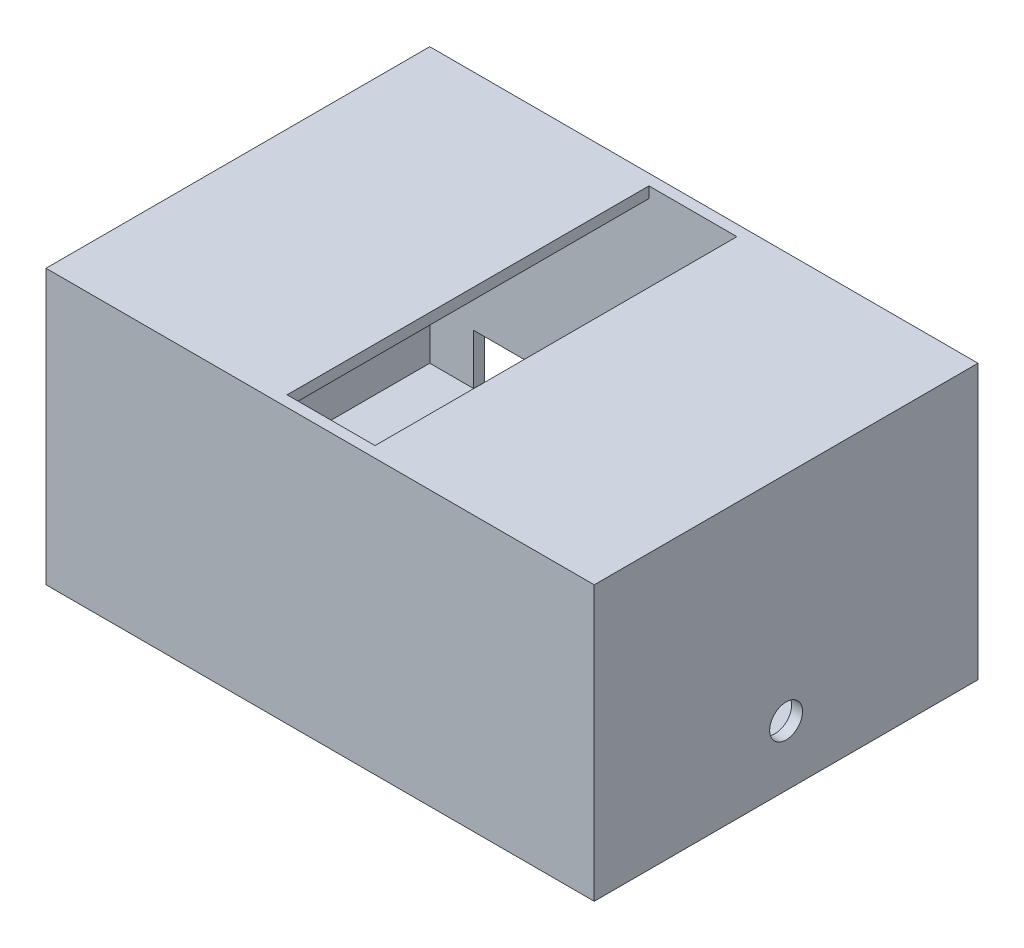
SolidWorks part; units mm, degrees
ref_plane "Front Plane" through (0, 0, 0) normal (0, 0, 1) x (1, 0, 0)
ref_plane "Top Plane" through (0, 0, 0) normal (0, 1, 0) x (1, 0, 0)
ref_plane "Right Plane" through (0, 0, 0) normal (1, 0, 0) x (0, 0, -1)
sketch "Sketch1" plane through (0, 0, 0) normal (0, 1, 0) x (1, 0, 0)
  line L0 (250, 0) -> (0, 0) construction
  line L1 (0, 0) -> (-250, 0) construction
  line L2 (-125, -87.5) -> (125, -87.5)
  line L3 (-125, -87.5) -> (-125, 87.5)
  line L4 (125, -87.5) -> (125, 87.5)
  line L5 (-125, 87.5) -> (125, 87.5)
  line L6 (-125, -87.5) -> (125, 87.5) construction
  line L7 (125, -87.5) -> (-125, 87.5) construction
  dimension "D1" = 175
  dimension "D2" = 250
extrude "Boss-Extrude1" add sketch "Sketch1" against normal blind 125
sketch "Sketch2" plane through (0, -125, 0) normal (0, -1, 0) x (1, 0, 0)
  line L0 (-125, 87.5) -> (125, 87.5) construction
  line L1 (-120, -82.5) -> (120, -82.5)
  line L2 (-120, -82.5) -> (-120, 82.5)
  line L3 (-120, 82.5) -> (120, 82.5)
  line L4 (120, -82.5) -> (120, 82.5)
  line L5 (-120, -82.5) -> (120, 82.5) construction
  line L6 (-120, 82.5) -> (120, -82.5) construction
  line L7 (125, 87.5) -> (125, -87.5) construction
  point P0 (0, 0)
  dimension "D1" = 5
  dimension "D2" = 5
extrude "Cut-Extrude1" cut sketch "Sketch2" against normal offset from surface (120 mm away) 5 up to face at (0, 0, 0)
sketch "Sketch3" plane through (0, 0, 0) normal (0, 1, 0) x (1, 0, 0)
  line L0 (-125, 0) -> (125, 0) construction
  line L1 (-125, 87.5) -> (-125, -87.5) construction
  line L2 (125, -87.5) -> (125, 87.5) construction
  line L3 (0, 87.5) -> (0, -120.2082) construction
  line L4 (-20.05, -82.5) -> (20.05, -82.5)
  line L5 (-20.05, -82.5) -> (-20.05, 82.5)
  line L6 (-20.05, 82.5) -> (20.05, 82.5)
  line L7 (20.05, -82.5) -> (20.05, 82.5)
  line L8 (-20.05, -82.5) -> (20.05, 82.5) construction
  line L9 (-20.05, 82.5) -> (20.05, -82.5) construction
  line L10 (125, 87.5) -> (-125, 87.5) construction
  point P6 (0, 0)
  dimension "D1" = 40.1
  dimension "D2" = 5
extrude "Cut-Extrude2" cut sketch "Sketch3" against normal through all
sketch "Sketch4" plane through (-125, 0, 0) normal (-1, 0, 0) x (0, 0, 1)
  line L0 (0, 0) -> (0, -125) construction
  line L1 (-87.5, -125) -> (87.5, -125) construction
  circle A0 centre (0, -97.5) radius 7.5
  point P7 (0, -62.5)
  point P8 (0, -62.5)
  point P10 (0, -97.5)
  dimension "D1" = 35
  dimension "D2" = 15
extrude "Cut-Extrude3" cut sketch "Sketch4" against normal through all
sketch "Sketch6" plane through (0, -125, 0) normal (0, -1, 0) x (1, 0, 0)
  line L1 (-125, 87.5) -> (125, 87.5)
  line L2 (-125, 87.5) -> (-125, -87.5)
  line L3 (-125, -87.5) -> (125, -87.5)
  line L4 (125, 87.5) -> (125, -87.5)
extrude "Boss-Extrude2" add sketch "Sketch6" against normal blind 5
sketch "Sketch7" plane through (0, 0, -87.5) normal (0, 0, -1) x (-1, 0, 0)
  line L0 (0, 0) -> (0, -125) construction
  line L1 (-125, -125) -> (125, -125) construction
  line L3 (-100, -120) -> (100, -120)
  line L4 (-100, -120) -> (-100, -97)
  line L5 (-100, -97) -> (100, -97)
  line L6 (100, -120) -> (100, -97)
  line L7 (-100, -120) -> (100, -97) construction
  line L8 (-100, -97) -> (100, -120) construction
  point P5 (0, -108.5)
  dimension "D1" = 200
  dimension "D2" = 23
  dimension "D3" = 5
extrude "Cut-Extrude4" cut sketch "Sketch7" against normal up to surface (5 mm away) up to face at (0, -32.5, -82.5)
